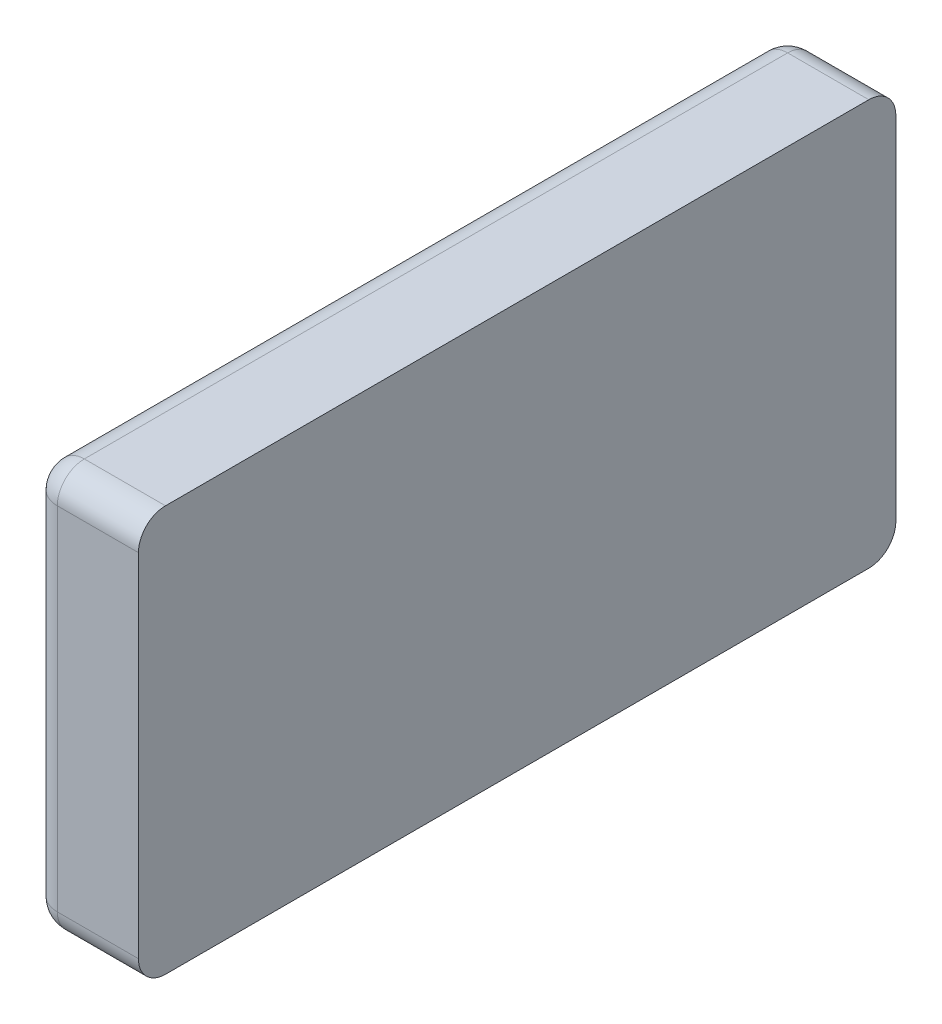
SolidWorks part; units mm, degrees
material "Ethafoam"
ref_plane "Płaszczyzna XY" through (0, 0, 0) normal (0, 0, 1) x (1, 0, 0)
ref_plane "Płaszczyzna XZ" through (0, 0, 0) normal (0, 1, 0) x (1, 0, 0)
ref_plane "Płaszczyzna YZ" through (0, 0, 0) normal (1, 0, 0) x (0, 0, -1)
sketch "Szkic1" plane through (1032.6, 0, 0) normal (-1, 0, 0) x (0, 0, 1)
  line L4 (622.51, 65) -> (622.51, -65)
  line L5 (632.51, -75) -> (892.51, -75)
  line L6 (902.51, -65) -> (902.51, 65)
  line L7 (892.51, 75) -> (632.51, 75)
  line L8 (622.51, 65) -> (622.51, -65)
  line L9 (632.51, -75) -> (892.51, -75)
  line L10 (902.51, -65) -> (902.51, 65)
  line L11 (892.51, 75) -> (632.51, 75)
  arc A4 (632.51, 75) -> (622.51, 65) centre (632.51, 65) ccw
  arc A5 (622.51, -65) -> (632.51, -75) centre (632.51, -65) ccw
  arc A6 (892.51, -75) -> (902.51, -65) centre (892.51, -65) ccw
  arc A7 (902.51, 65) -> (892.51, 75) centre (892.51, 65) ccw
  arc A8 (632.51, 75) -> (622.51, 65) centre (632.51, 65) ccw
  arc A9 (622.51, -65) -> (632.51, -75) centre (632.51, -65) ccw
  arc A10 (892.51, -75) -> (902.51, -65) centre (892.51, -65) ccw
  arc A11 (902.51, 65) -> (892.51, 75) centre (892.51, 65) ccw
  dimension "D1" = 0
extrude "Dodanie-wyciągnięcie1" add sketch "Szkic1" along normal blind 40
fillet "Zaokrąglenie1" radius 10 8 edges at (992.6, -72.0711, 899.5811) (992.6, -75, 762.51) (992.6, -72.0711, 625.4389) (992.6, 0, 622.51) (992.6, 72.0711, 625.4389) (992.6, 75, 762.51) (992.6, 72.0711, 899.5811) (992.6, 0, 902.51)
